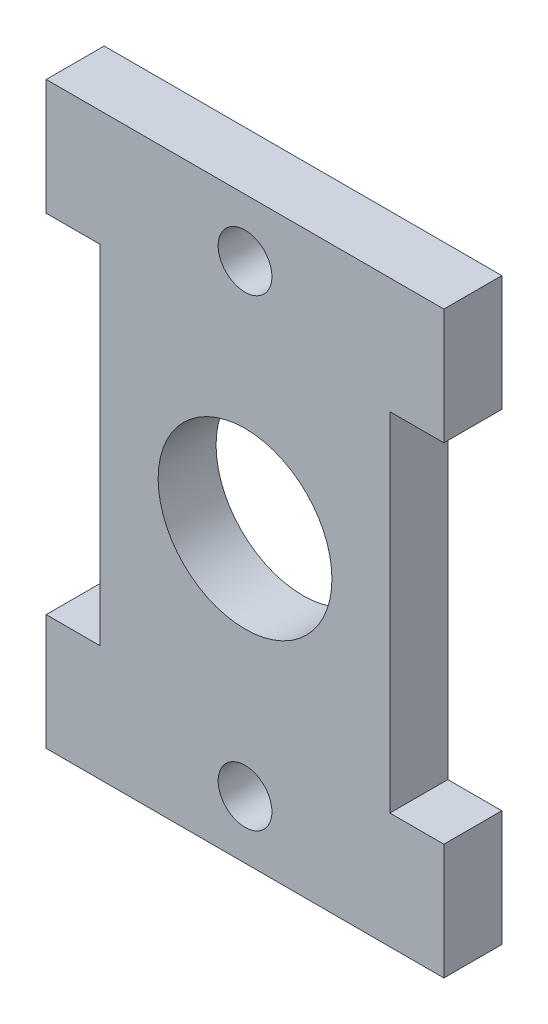
SolidWorks part; units mm, degrees
ref_plane "Front Plane" through (0, 0, 0) normal (0, 0, 1) x (1, 0, 0)
ref_plane "Top Plane" through (0, 0, 0) normal (0, 1, 0) x (1, 0, 0)
ref_plane "Right Plane" through (0, 0, 0) normal (1, 0, 0) x (0, 0, -1)
sketch "Sketch1" plane through (0, 0, 0) normal (0, 0, 1) x (1, 0, 0)
  line L0 (7.9375, -3.175) -> (10.8966, -3.175)
  line L1 (-10.8966, 3.175) -> (10.8966, 3.175)
  line L2 (-10.8966, 3.175) -> (-10.8966, -3.175)
  line L3 (-10.8966, -3.175) -> (-7.9375, -3.175)
  line L4 (10.8966, 3.175) -> (10.8966, -3.175)
  line L5 (-10.8966, 3.175) -> (10.8966, -3.175) construction
  line L6 (-10.8966, -3.175) -> (10.8966, 3.175) construction
  line L7 (-12.7, -12.7) -> (12.7, -12.7) construction
  line L8 (-7.9375, -3.175) -> (-7.9375, -22.225)
  line L9 (0, -3.9078) -> (0, -8.5431) construction
  line L10 (7.9375, -3.175) -> (7.9375, -22.225)
  line L11 (0, -21.4922) -> (0, -16.8569) construction
  line L12 (-10.8966, -22.225) -> (10.8966, -28.575) construction
  line L13 (-10.8966, -28.575) -> (10.8966, -22.225) construction
  line L14 (10.8966, -28.575) -> (10.8966, -22.225)
  line L15 (-10.8966, -22.225) -> (-7.9375, -22.225)
  line L16 (-10.8966, -28.575) -> (-10.8966, -22.225)
  line L17 (-10.8966, -28.575) -> (10.8966, -28.575)
  line L18 (7.9375, -22.225) -> (10.8966, -22.225)
  point P0 (0, 0)
  point P8 (0, -25.4)
  point P21 (7.9375, -12.7)
  point P22 (-7.9375, -12.7)
  dimension "D1" = 6.35
  dimension "D2" = 2.9591
  dimension "D3" = 15.875
  dimension "D5" = 15.875
extrude "Boss-Extrude1" add sketch "Sketch1" along normal blind 3.175
hole_wizard "#4 Clearance Hole1" positions "Sketch3" profile "Sketch2" hole size "#4" standard "ANSI Inch"
sketch "Sketch3" plane through (0, 0, 3.175) normal (0, 0, 1) x (1, 0, 0)
  point P0 (0, 0)
  point P5 (0, -25.4)
sketch "Sketch2" plane through (0, 0, 3.175) normal (1, 0, 0) x (0, -1, 0)
  line L0 (0, 0) -> (0, 4.1872)
  line L1 (0, 4.1872) -> (1.4732, 3.302)
  line L2 (1.4732, 3.302) -> (1.4732, 0)
  line L5 (1.4732, 0) -> (0, 0)
  line L10 (0, 4.1872) -> (-1.4732, 3.302) construction
  line L11 (0, -6.35) -> (0, 107.95) construction
  dimension "Hole Dia." = 2.9464
  dimension "Hole Depth" = 3.302
  dimension "Drill Angle" = 118
sketch "Sketch4" plane through (0, 0, 3.175) normal (0, 0, 1) x (1, 0, 0)
  line L0 (-7.9375, -3.175) -> (-7.9375, -22.225) construction
  circle A0 centre (0, -12.7) radius 4.7625
  point P4 (-7.9375, -12.7)
  dimension "D1" = 9.525
extrude "Cut-Extrude1" cut sketch "Sketch4" against normal up to next contours A0
